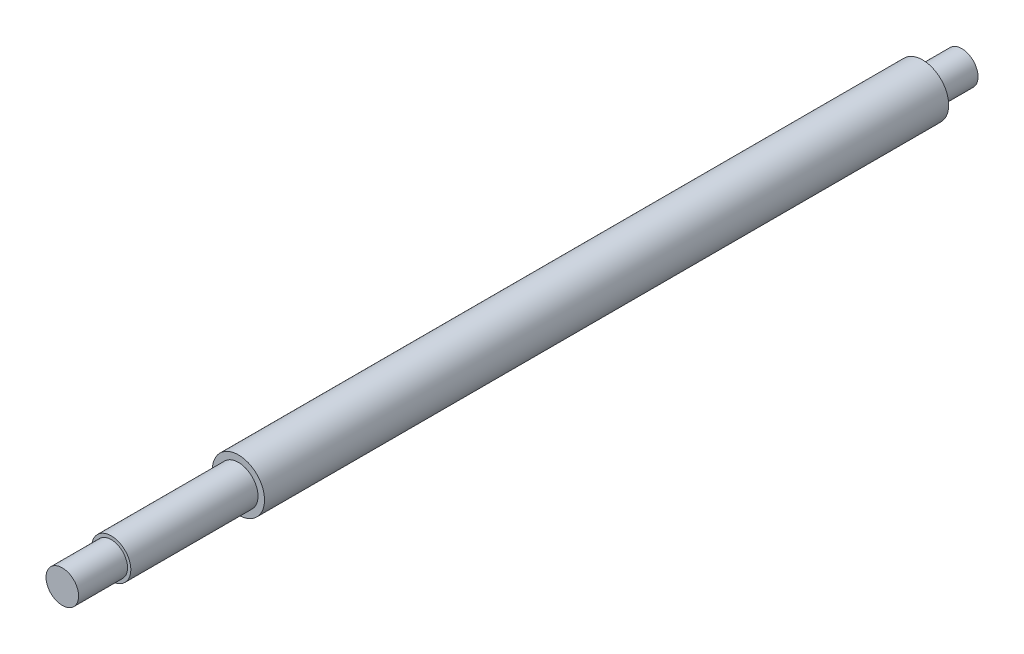
SolidWorks part; units mm, degrees
ref_plane "Front Plane" through (0, 0, 0) normal (0, 0, 1) x (1, 0, 0)
ref_plane "Top Plane" through (0, 0, 0) normal (0, 1, 0) x (1, 0, 0)
ref_plane "Right Plane" through (0, 0, 0) normal (1, 0, 0) x (0, 0, -1)
sketch "Sketch1" plane through (0, 0, 0) normal (1, 0, 0) x (0, 0, -1)
  line L0 (0, 0) -> (-42.623, 0) construction
  line L1 (-480.75, 0) -> (-480.75, 5)
  line L2 (-480.75, 5) -> (-465.75, 5)
  line L3 (-465.75, 5) -> (-465.75, 6)
  line L4 (-465.75, 6) -> (-426.75, 6)
  line L5 (-426.75, 6) -> (-426.75, 8)
  line L6 (-426.75, 8) -> (-12, 8)
  line L7 (-12, 8) -> (-12, 5)
  line L8 (-12, 5) -> (0, 5)
  line L9 (0, 5) -> (0, 0)
  line L10 (-480.75, 0) -> (0, 0)
  dimension "D1" = 5
  dimension "D2" = 6
  dimension "D3" = 8
  dimension "D4" = 5
  dimension "D5" = 12
  dimension "D6" = 39
  dimension "D7" = 15
  dimension "D8" = 414.75
revolve "Revolve1" [suppressed] add sketch "Sketch1" angle 360 about L0
sketch "Sketch3" plane through (0, 0, 0) normal (1, 0, 0) x (0, 0, -1)
  line L0 (-80.9254, 0) -> (-123.5483, 0) construction
  line L1 (-275.75, 0) -> (-275.75, 5)
  line L2 (-275.75, 5) -> (-260.75, 5)
  line L3 (-260.75, 5) -> (-260.75, 6)
  line L4 (-260.75, 6) -> (-221.75, 6)
  line L5 (-221.75, 6) -> (-221.75, 8)
  line L6 (-221.75, 8) -> (-12, 8)
  line L7 (-12, 8) -> (-12, 5)
  line L8 (-12, 5) -> (0, 5)
  line L9 (0, 5) -> (0, 0)
  line L10 (-275.75, 0) -> (0, 0)
  point P12 (0, 0)
  point P14 (0, 0)
  dimension "D1" = 10
  dimension "D2" = 6
  dimension "D3" = 8
  dimension "D4" = 10
  dimension "D5" = 15
  dimension "D6" = 39
  dimension "D7" = 209.75
  dimension "D8" = 12
revolve "Revolve2" add sketch "Sketch3" angle 360 about L0
